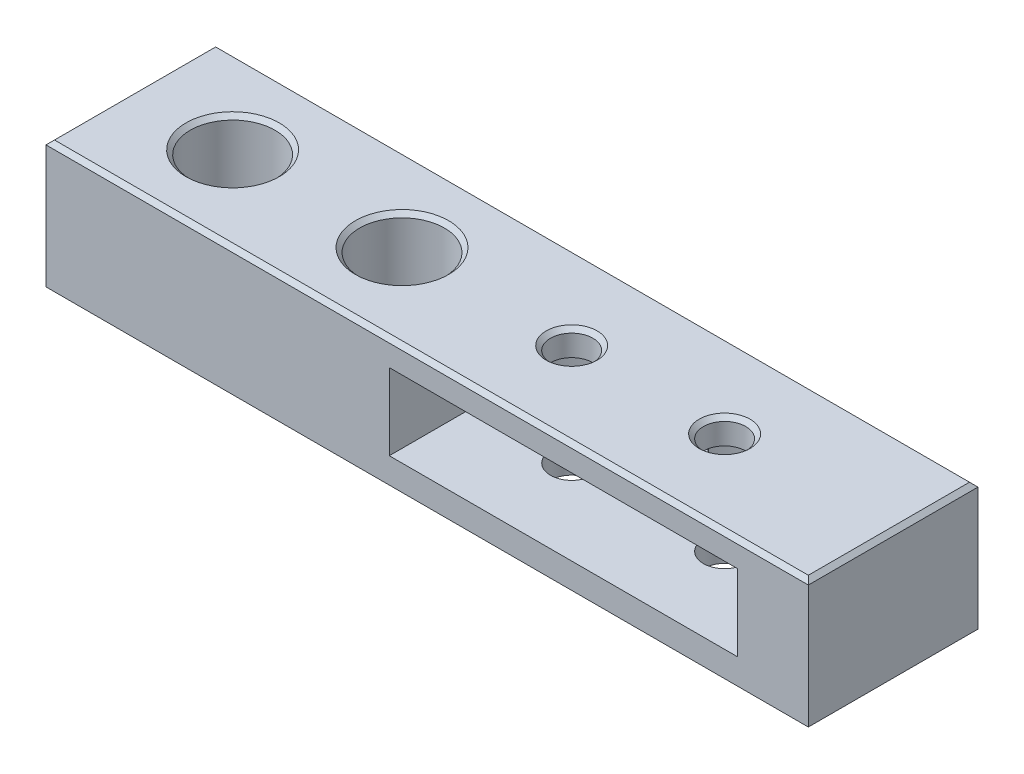
SolidWorks part; units mm, degrees
ref_plane "Front Plane" through (0, 0, 0) normal (0, 0, 1) x (1, 0, 0)
ref_plane "Top Plane" through (0, 0, 0) normal (0, 1, 0) x (1, 0, 0)
ref_plane "Right Plane" through (0, 0, 0) normal (1, 0, 0) x (0, 0, -1)
sketch "Sketch1" plane through (0, 0, 0) normal (0, 1, 0) x (1, 0, 0)
  line L0 (0, 0) -> (-70, 0) construction
  line L2 (-70, 10) -> (11.37, 10)
  line L3 (-70, 10) -> (-70, -10)
  line L4 (-70, -10) -> (11.37, -10)
  line L5 (11.37, 10) -> (11.37, -10)
  line L6 (-70, 10) -> (11.37, -10) construction
  line L7 (-70, -10) -> (11.37, 10) construction
  circle A0 centre (0, 0) radius 2.5
  circle A1 centre (-18.03, 0) radius 2.5
  point P3 (-29.315, 0)
  dimension "D1" = 5
  dimension "D2" = 20
  dimension "D3" = 11.37
  dimension "D4" = 70
  dimension "D5" = 18.03
extrude "Boss-Extrude1" add sketch "Sketch1" along normal blind 15
sketch "Sketch2" plane through (0, 15, 0) normal (0, 1, 0) x (1, 0, 0)
  line L0 (0, 0) -> (-70, 0) construction
  line L1 (-70, 10) -> (-70, -10) construction
  circle A0 centre (0, 0) radius 9.017
  circle A2 centre (-18.03, 0) radius 9.013
  point P5 (-58, 0)
  point P6 (-38.03, 0)
  point P10 (-37.0086, 0)
  dimension "D2" = 18.034
  dimension "D3" = 20
  dimension "D1" = 12
hole_wizard "CBORE for M5 SHCS1" positions "Sketch4" profile "Sketch5" counterbore size "M5" standard "ANSI Metric" end condition through all
sketch "Sketch4" plane through (0, 15, 0) normal (0, 1, 0) x (1, 0, 0)
  point P0 (-58, 0)
  point P3 (-38.03, 0)
sketch "Sketch5" plane through (-58, 15, 0) normal (1, 0, 0) x (0, 0, 1)
  line L0 (0, 0) -> (0, 15)
  line L1 (0, 15) -> (2.75, 15)
  line L3 (2.75, 15) -> (2.75, 10)
  line L4 (2.75, 10) -> (5, 10)
  line L5 (5, 10) -> (5, 0)
  line L7 (5, 0) -> (0, 0)
  line L11 (0, -6.35) -> (0, 107.95) construction
  dimension "Thru Hole Dia." = 5.5
  dimension "Thru Hole Depth" = 15
  dimension "C'Bore Dia." = 10
  dimension "C'Bore Depth" = 10
sketch "Sketch8" plane through (11.37, 0, 0) normal (1, 0, 0) x (0, 0, -1)
  line L4 (-10, 0) -> (10, 0)
  line L5 (10, 0) -> (10, 15)
  line L6 (10, 15) -> (-10, 15)
  line L7 (-10, 15) -> (-10, 0)
  line L8 (-10, 0) -> (10, 0)
  line L9 (10, 0) -> (10, 15)
  line L10 (10, 15) -> (-10, 15)
  line L11 (-10, 15) -> (-10, 0)
  dimension "D1" = 0
extrude "Boss-Extrude3" add sketch "Sketch8" along normal blind 8.5
sketch "Sketch6" plane through (0, 15, 0) normal (0, 1, 0) x (1, 0, 0)
  line L1 (-29.53, 0) -> (-29.53, -10)
  line L4 (11.5, 0) -> (11.5, -10)
  line L5 (-70, -10) -> (19.87, -10) construction
  line L6 (11.5, -10) -> (-29.53, -10)
  arc A2 (-9.015, 7.14) -> (11.5, 0) centre (0, 0) cw
  arc A3 (-9.015, 7.14) -> (-29.53, 0) centre (-18.03, 0) ccw
  point P1 (0, 0)
  point P14 (-26.4635, -3.8702)
  point P18 (-27.3969, -10)
  dimension "D1" = 11.5
extrude "Cut-Extrude1" cut sketch "Sketch6" against normal blind 9 from offset 3 offset against normal yes
sketch "Sketch7" plane through (0, 0, 0) normal (0, -1, 0) x (1, 0, 0)
  line L0 (11.37, 0) -> (-70, 0) construction
  line L2 (-70, -10) -> (-70, 10) construction
  line L4 (-9, -3.05) -> (-14, -3.05)
  line L5 (-9, -3.05) -> (-9, 3.05)
  line L6 (-9, 3.05) -> (-14, 3.05)
  line L7 (-14, -3.05) -> (-14, 3.05)
  line L8 (-9, -3.05) -> (-14, 3.05) construction
  line L9 (-9, 3.05) -> (-14, -3.05) construction
  line L10 (-65, -3.05) -> (-70, -3.05)
  line L11 (-65, -3.05) -> (-65, 3.05)
  line L12 (-65, 3.05) -> (-70, 3.05)
  line L13 (-70, -3.05) -> (-70, 3.05)
  line L14 (-65, -3.05) -> (-70, 3.05) construction
  line L15 (-65, 3.05) -> (-70, -3.05) construction
  point P2 (-13.876, 3)
  point P3 (-24.5163, 0)
  point P6 (-11.5, 0)
  point P11 (-67.5, 0)
  dimension "D1" = 5
  dimension "D2" = 6.1
  dimension "D3" = 56
extrude "Boss-Extrude2" add sketch "Sketch7" along normal blind 4
chamfer "Chamfer1" distance 0.5 angle 45 8 edges at (0, 15, 2.5) (-25.065, 15, 10) (-70, 15, 0) (-25.065, 15, -10) (-38.03, 15, 5) (-58, 15, 5) (-18.03, 15, 2.5) (19.87, 15, 0)
